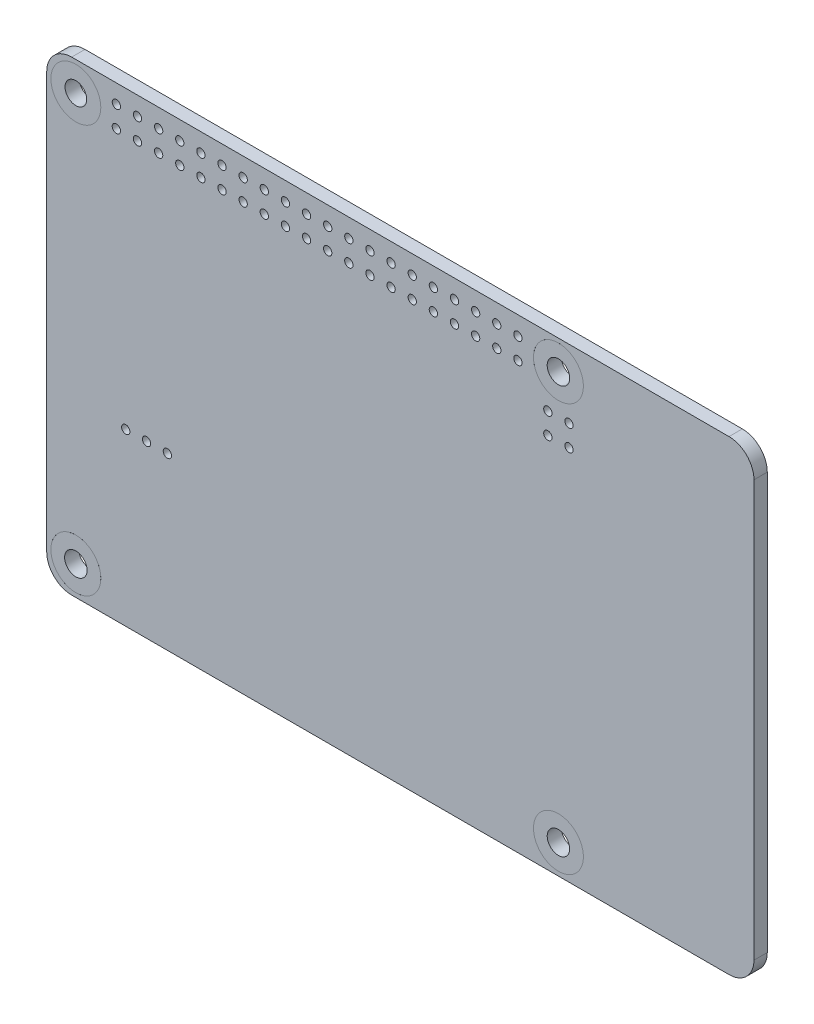
SolidWorks part; units mm, degrees
material "ABS"
ref_plane "Płaszczyzna przednia" through (0, 0, 0) normal (0, 0, 1) x (1, 0, 0)
ref_plane "Płaszczyzna górna" through (0, 0, 0) normal (0, 1, 0) x (1, 0, 0)
ref_plane "Płaszczyzna prawa" through (0, 0, 0) normal (1, 0, 0) x (0, 0, -1)
sketch "Sketch1" plane through (0, 0, 0) normal (0, 0, 1) x (1, 0, 0)
  line L0 (-39.5, -28) -> (39.5, -28)
  line L1 (42.5, -25) -> (42.5, 25)
  line L2 (39.5, 28) -> (-39.5, 28)
  line L3 (-42.5, 25) -> (-42.5, -25)
  line L4 (0, -28) -> (0, 28) construction
  arc A0 (39.5, -28) -> (42.5, -25) centre (39.5, -25) ccw
  arc A1 (42.5, 25) -> (39.5, 28) centre (39.5, 25) ccw
  arc A2 (-39.5, 28) -> (-42.5, 25) centre (-39.5, 25) ccw
  arc A3 (-42.5, -25) -> (-39.5, -28) centre (-39.5, -25) ccw
  dimension "D3" = 3
  dimension "D1" = 85
  dimension "D2" = 56
extrude "Boss-Extrude1" add sketch "Sketch1" along normal blind 1.6
sketch "Sketch3" plane through (0, 0, 1.6) normal (0, 0, 1) x (1, 0, 0)
  line L0 (-39, 28) -> (-39, 24.5) construction
  line L1 (39.5, 28) -> (-39.5, 28) construction
  line L2 (-39, 24.5) -> (-42.5, 24.5) construction
  line L4 (-42.5, 25) -> (-42.5, -25) construction
  line L5 (-42.5, 0) -> (-59.0247, 0) construction
  line L6 (-39, -24.5) -> (-42.5, -24.5) construction
  line L7 (-39, -28) -> (-39, -24.5) construction
  line L8 (-39, 24.5) -> (19, 24.5) construction
  line L9 (-10, 24.5) -> (-10, 38.9461) construction
  line L10 (19, -28) -> (19, -24.5) construction
  line L11 (19, -24.5) -> (22.5, -24.5) construction
  line L12 (22.5, 0) -> (39.0247, 0) construction
  line L13 (19, 24.5) -> (22.5, 24.5) construction
  line L14 (19, 28) -> (19, 24.5) construction
  circle A1 centre (-39, 24.5) radius 3
  circle A2 centre (-39, -24.5) radius 3
  circle A3 centre (19, -24.5) radius 3
  circle A4 centre (19, 24.5) radius 3
  dimension "D3" = 58
  dimension "D1" = 3.5
  dimension "D2" = 3.5
extrude "Cut-Extrude1" cut sketch "Sketch3" against normal through all
sketch "Sketch4" plane through (0, 0, 1.6) normal (0, 0, 1) x (1, 0, 0)
  circle A0 centre (-39, -24.5) radius 3 construction
  circle A1 centre (19, -24.5) radius 3 construction
  circle A2 centre (19, 24.5) radius 3 construction
  circle A3 centre (-39, 24.5) radius 3 construction
  circle A4 centre (-39, -24.5) radius 3
  circle A5 centre (19, -24.5) radius 3
  circle A6 centre (19, 24.5) radius 3
  circle A7 centre (-39, 24.5) radius 3
  circle A8 centre (-39, -24.5) radius 1.35
  circle A9 centre (19, -24.5) radius 1.35
  circle A10 centre (19, 24.5) radius 1.35
  circle A11 centre (-39, 24.5) radius 1.3
  dimension "D1" = 2.6
extrude "Boss-Extrude2" add sketch "Sketch4" against normal blind 1.7 separate body
sketch "Sketch5" plane through (0, 0, 1.6) normal (0, 0, 1) x (1, 0, 0)
  line L0 (-33, -28) -> (-33, -7.5) construction
  line L1 (-39.5, -28) -> (39.5, -28) construction
  line L2 (-42.5, -7.5) -> (-33, -7.5) construction
  line L3 (-42.5, 25) -> (-42.5, -25) construction
  line L4 (-33, -7.5) -> (-30.5, -7.5) construction
  line L5 (-30.5, -7.5) -> (-28, -7.5) construction
  circle A0 centre (-33, -7.5) radius 0.5
  circle A1 centre (-30.5, -7.5) radius 0.5
  circle A2 centre (-28, -7.5) radius 0.5
  dimension "D1" = 9.5
  dimension "D2" = 20.5
extrude "Cut-Extrude2" cut sketch "Sketch5" against normal through all
sketch "Sketch6" plane through (0, 0, 1.6) normal (0, 0, 1) x (1, 0, 0)
  line L0 (39.5, 28) -> (-39.5, 28) construction
  line L1 (-42.5, 25) -> (-42.5, -25) construction
  circle A0 centre (-34.13, 25.77) radius 0.5
  circle A1 centre (-34.13, 23.23) radius 0.5
  circle A2 centre (-31.59, 25.77) radius 0.5
  circle A3 centre (-31.59, 23.23) radius 0.5
  circle A4 centre (-29.05, 25.77) radius 0.5
  circle A5 centre (-29.05, 23.23) radius 0.5
  circle A6 centre (-26.51, 25.77) radius 0.5
  circle A7 centre (-26.51, 23.23) radius 0.5
  circle A8 centre (-23.97, 25.77) radius 0.5
  circle A9 centre (-23.97, 23.23) radius 0.5
  circle A10 centre (-21.43, 25.77) radius 0.5
  circle A11 centre (-21.43, 23.23) radius 0.5
  circle A12 centre (-18.89, 25.77) radius 0.5
  circle A13 centre (-18.89, 23.23) radius 0.5
  circle A14 centre (-16.35, 25.77) radius 0.5
  circle A15 centre (-16.35, 23.23) radius 0.5
  circle A16 centre (-13.81, 25.77) radius 0.5
  circle A17 centre (-13.81, 23.23) radius 0.5
  circle A18 centre (-11.27, 25.77) radius 0.5
  circle A19 centre (-11.27, 23.23) radius 0.5
  circle A20 centre (-8.73, 25.77) radius 0.5
  circle A21 centre (-8.73, 23.23) radius 0.5
  circle A22 centre (-6.19, 25.77) radius 0.5
  circle A23 centre (-6.19, 23.23) radius 0.5
  circle A24 centre (-3.65, 25.77) radius 0.5
  circle A25 centre (-3.65, 23.23) radius 0.5
  circle A26 centre (-1.11, 25.77) radius 0.5
  circle A27 centre (-1.11, 23.23) radius 0.5
  circle A28 centre (1.43, 25.77) radius 0.5
  circle A29 centre (1.43, 23.23) radius 0.5
  circle A30 centre (3.97, 25.77) radius 0.5
  circle A31 centre (3.97, 23.23) radius 0.5
  circle A32 centre (6.51, 25.77) radius 0.5
  circle A33 centre (6.51, 23.23) radius 0.5
  circle A34 centre (9.05, 25.77) radius 0.5
  circle A35 centre (9.05, 23.23) radius 0.5
  circle A36 centre (11.59, 25.77) radius 0.5
  circle A37 centre (11.59, 23.23) radius 0.5
  circle A38 centre (14.13, 25.77) radius 0.5
  circle A39 centre (14.13, 23.23) radius 0.5
  dimension "D1" = 2.54
  dimension "D2" = 1
  dimension "D3" = 2.23
  dimension "D4" = 8.37
  dimension "D5" = 20
extrude "Cut-Extrude3" cut sketch "Sketch6" against normal through all
sketch "Sketch7" plane through (0, 0, 1.6) normal (0, 0, 1) x (1, 0, 0)
  line L0 (42.5, -25) -> (42.5, 25) construction
  line L1 (39.5, 28) -> (-39.5, 28) construction
  circle A0 centre (20.27, 19.77) radius 0.5
  circle A1 centre (17.73, 19.77) radius 0.5
  circle A2 centre (17.73, 17.23) radius 0.5
  circle A3 centre (20.27, 17.23) radius 0.5
  dimension "D1" = 22.23
  dimension "D2" = 8.23
  dimension "D3" = 2.54
  dimension "D4" = 2.54
  dimension "D5" = 1
extrude "Cut-Extrude4" cut sketch "Sketch7" against normal through all
